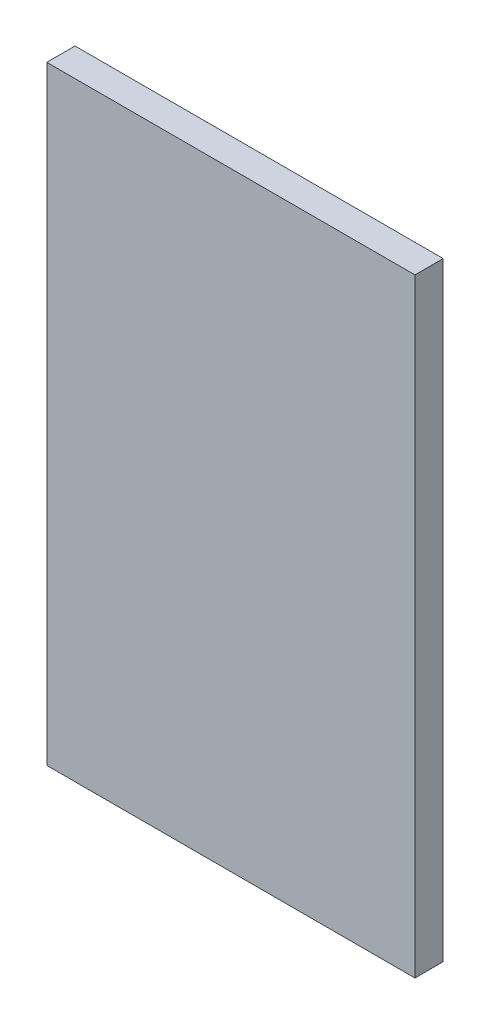
SolidWorks part; units mm, degrees
ref_plane "Front Plane" through (0, 0, 0) normal (0, 0, 1) x (1, 0, 0)
ref_plane "Top Plane" through (0, 0, 0) normal (0, 1, 0) x (1, 0, 0)
ref_plane "Right Plane" through (0, 0, 0) normal (1, 0, 0) x (0, 0, -1)
sketch "Sketch2" plane through (0, 0, 0) normal (0, 0, 1) x (1, 0, 0)
  line L0 (-32.7273, 70.5301) -> (32.4146, 70.5301)
  line L1 (-32.7273, 70.5301) -> (-32.7273, -37.2054)
  line L2 (32.4146, 70.5301) -> (32.4146, -37.2054)
  line L3 (-32.7273, -37.2054) -> (32.4146, -37.2054)
extrude "Boss-Extrude1" add sketch "Sketch2" along normal blind 5
